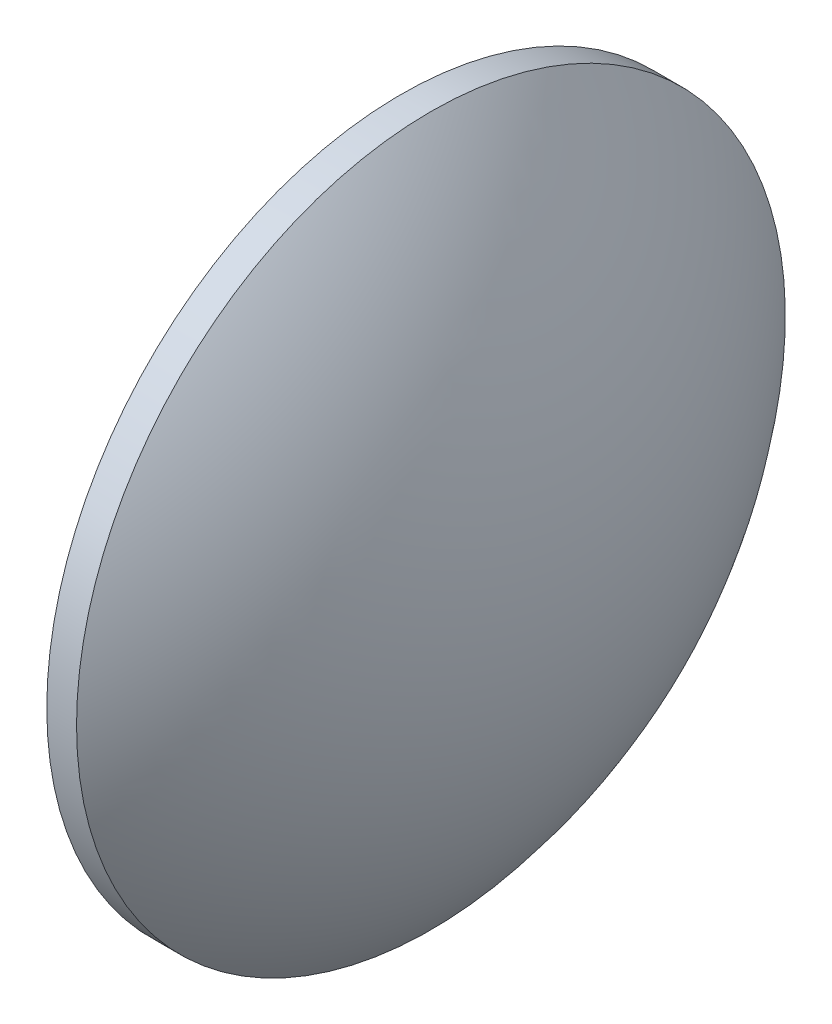
SolidWorks part; units mm, degrees
ref_plane "前视基准面" through (0, 0, 0) normal (0, 0, 1) x (1, 0, 0)
ref_plane "上视基准面" through (0, 0, 0) normal (0, 1, 0) x (1, 0, 0)
ref_plane "右视基准面" through (0, 0, 0) normal (1, 0, 0) x (0, 0, -1)
sketch "草图1" plane through (0, 0, 0) normal (0, 0, 1) x (1, 0, 0)
  line L0 (496.9109, 160.8342) -> (510.3567, 160.8342) construction
  line L1 (501.5675, 160.8342) -> (501.5675, 170.8342)
  line L2 (506.0675, 160.8342) -> (501.5675, 160.8342)
  line L5 (501.5675, 170.8342) -> (502.4075, 170.8342)
  arc A0 (506.0675, 160.8342) -> (502.4075, 170.8342) centre (490.5763, 160.8342) ccw
revolve "旋转1" add sketch "草图1" angle 360 about L0
